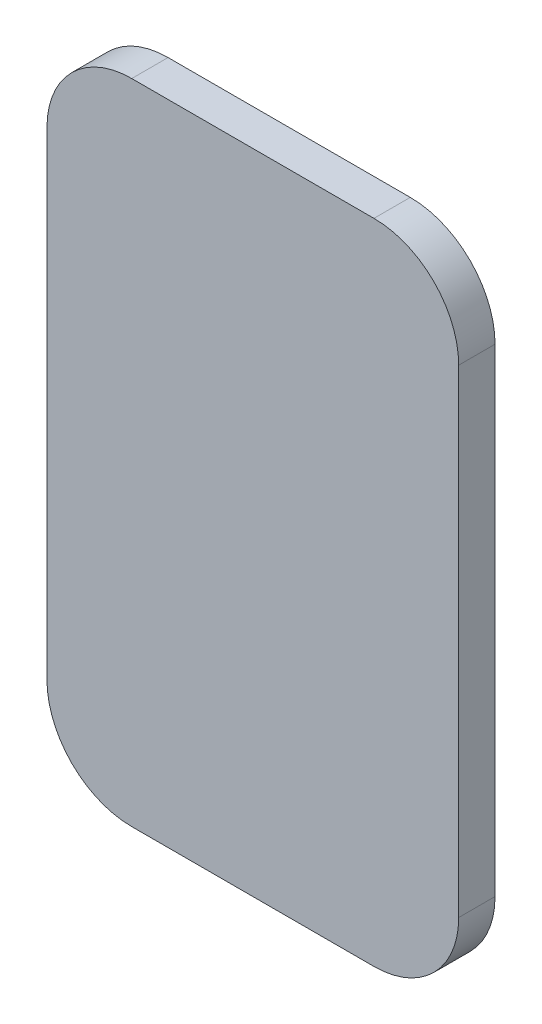
SolidWorks part; units mm, degrees
material "PC High Viscosity"
ref_plane "Front Plane" through (0, 0, 0) normal (0, 0, 1) x (1, 0, 0)
ref_plane "Top Plane" through (0, 0, 0) normal (0, 1, 0) x (1, 0, 0)
ref_plane "Right Plane" through (0, 0, 0) normal (1, 0, 0) x (0, 0, -1)
sketch "Sketch1" plane through (0, 0, 0) normal (0, 0, 1) x (1, 0, 0)
  line L8 (-94.7, 58.985) -> (-94.7, -20.015)
  line L9 (-80.7, -34.015) -> (-40.7, -34.015)
  line L10 (-26.7, -20.015) -> (-26.7, 58.985)
  line L11 (-40.7, 72.985) -> (-80.7, 72.985)
  line L12 (-94.7, 58.985) -> (-94.7, -20.015)
  line L13 (-80.7, -34.015) -> (-40.7, -34.015)
  line L14 (-26.7, -20.015) -> (-26.7, 58.985)
  line L15 (-40.7, 72.985) -> (-80.7, 72.985)
  arc A8 (-94.7, -20.015) -> (-80.7, -34.015) centre (-80.7, -20.015) ccw
  arc A9 (-40.7, -34.015) -> (-26.7, -20.015) centre (-40.7, -20.015) ccw
  arc A10 (-26.7, 58.985) -> (-40.7, 72.985) centre (-40.7, 58.985) ccw
  arc A11 (-80.7, 72.985) -> (-94.7, 58.985) centre (-80.7, 58.985) ccw
  arc A12 (-94.7, -20.015) -> (-80.7, -34.015) centre (-80.7, -20.015) ccw
  arc A13 (-40.7, -34.015) -> (-26.7, -20.015) centre (-40.7, -20.015) ccw
  arc A14 (-26.7, 58.985) -> (-40.7, 72.985) centre (-40.7, 58.985) ccw
  arc A15 (-80.7, 72.985) -> (-94.7, 58.985) centre (-80.7, 58.985) ccw
  dimension "D1" = 8
extrude "Boss-Extrude1" add sketch "Sketch1" along normal blind 6
